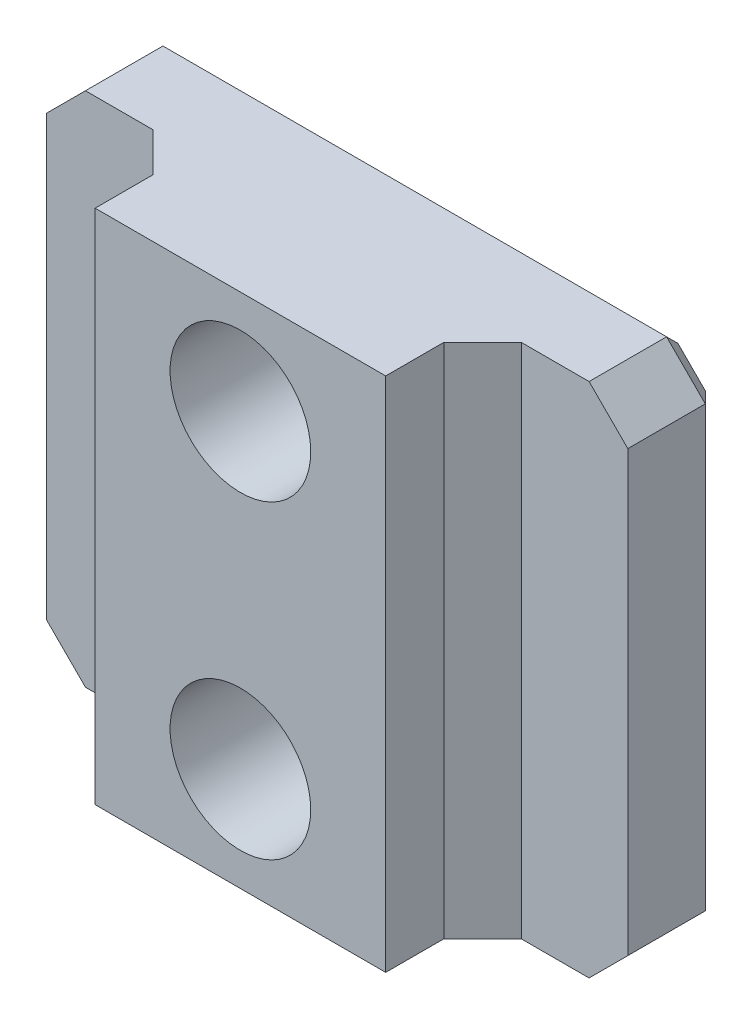
SolidWorks part; units mm, degrees
material "PET"
ref_plane "Front Plane" through (0, 0, 0) normal (0, 0, 1) x (1, 0, 0)
ref_plane "Top Plane" through (0, 0, 0) normal (0, 1, 0) x (1, 0, 0)
ref_plane "Right Plane" through (0, 0, 0) normal (1, 0, 0) x (0, 0, -1)
sketch "Sketch1" plane through (0, 0, 0) normal (0, 0, 1) x (1, 0, 0)
  line L4 (-143.0545, 4.4787) -> (-104.9545, 4.4787)
  line L5 (-104.9545, 4.4787) -> (-104.9545, 38.3463)
  line L6 (-104.9545, 38.3463) -> (-143.0545, 38.3463)
  line L7 (-143.0545, 38.3463) -> (-143.0545, 4.4787)
  line L8 (-143.0545, 4.4787) -> (-104.9545, 4.4787)
  line L9 (-104.9545, 4.4787) -> (-104.9545, 38.3463)
  line L10 (-104.9545, 38.3463) -> (-143.0545, 38.3463)
  line L11 (-143.0545, 38.3463) -> (-143.0545, 4.4787)
  dimension "D1" = 0
extrude "Boss-Extrude1" add sketch "Sketch1" along normal blind 12.7
hole_wizard "1/4 Clearance Hole1" positions "Sketch4" profile "Sketch6" hole size "1/4" standard "ANSI Inch" end condition through all
sketch "Sketch4" plane through (0, 0, 0) normal (0, 0, -1) x (-1, 0, 0)
  point P0 (124.0045, 11.2525)
  point P3 (124.0045, 31.5725)
sketch "Sketch6" plane through (-124.0045, 11.2525, 0) normal (1, 0, 0) x (0, 1, 0)
  line L0 (0, 0) -> (0, 12.7)
  line L1 (0, 12.7) -> (3.5712, 12.7)
  line L2 (3.5712, 12.7) -> (3.5712, 0)
  line L5 (3.5712, 0) -> (0, 0)
  line L11 (0, -6.35) -> (0, 107.95) construction
  dimension "Thru Hole Dia." = 7.1425
  dimension "Thru Hole Depth" = 12.7
hole_wizard "Hole1" positions "3DSketch1" profile "Sketch8" legacy
sketch3d "3DSketch1"
  point P9 (-124.0045, 11.2525, 12.7)
  point P11 (-124.0045, 31.5725, 12.7)
sketch "Sketch8" plane through (-124.0045, 11.2525, 12.7) normal (1, 0, 0) x (0, -1, 0)
  line L0 (0, 0) -> (0, 7.62)
  line L1 (0, 7.62) -> (4.4323, 7.62)
  line L2 (4.4323, 7.62) -> (4.6101, 0)
  line L3 (4.6101, 0) -> (0, 0)
  line L4 (0, 110) -> (0, -10) construction
  dimension "Minor Diameter" = 8.8646
  dimension "Depth" = 7.62
  dimension "Major Diameter" = 9.2202
sketch "Sketch9" plane through (0, 4.4787, 0) normal (0, -1, 0) x (1, 0, 0)
  line L5 (-143.0545, 12.7) -> (-104.9545, 12.7) construction
  line L6 (-124.0045, 0) -> (-124.0045, 12.7) construction
  line L7 (-104.9545, 0) -> (-143.0545, 0) construction
  line L8 (-124.0045, 12.7) -> (-104.9545, 12.7) construction
  line L9 (-104.9545, 12.7) -> (-104.9545, 0) construction
  line L10 (-104.9545, 6.35) -> (-114.4795, 6.35)
  line L11 (-104.9545, 6.35) -> (-104.9545, 12.7)
  line L12 (-104.9545, 12.7) -> (-114.4795, 12.7)
  line L13 (-114.4795, 6.35) -> (-114.4795, 12.7)
  line L14 (-133.5295, 6.35) -> (-133.5295, 12.7)
  line L15 (-143.0545, 12.7) -> (-133.5295, 12.7)
  line L16 (-143.0545, 6.35) -> (-143.0545, 12.7)
  line L17 (-143.0545, 6.35) -> (-133.5295, 6.35)
extrude "Cut-Extrude1" cut sketch "Sketch9" against normal through all
chamfer "Chamfer1" distance 2.54 angle 45 6 edges at (-143.0545, 38.3463, 3.175) (-104.9545, 38.3463, 3.175) (-143.0545, 4.4787, 3.175) (-104.9545, 4.4787, 3.175) (-133.5295, 21.4125, 6.35) (-114.4795, 21.4125, 6.35)
chamfer "Chamfer2" distance 1.27 angle 45 8 edges at (-141.7845, 5.7487, 0) (-124.0045, 4.4787, 0) (-106.2245, 5.7487, 0) (-104.9545, 21.4125, 0) (-106.2245, 37.0763, 0) (-124.0045, 38.3463, 0) (-141.7845, 37.0763, 0) (-143.0545, 21.4125, 0)
